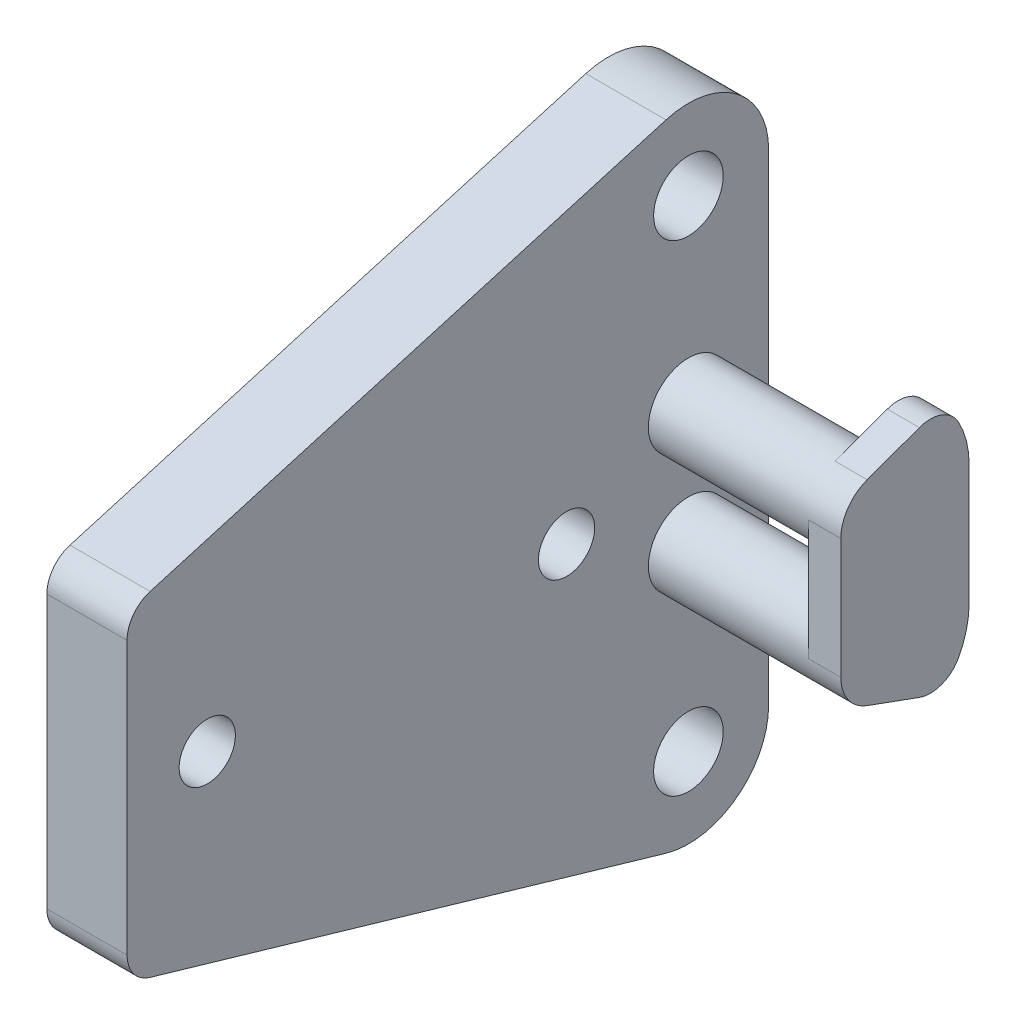
SolidWorks part; units mm, degrees
ref_plane "Front Plane" through (0, 0, 0) normal (0, 0, 1) x (1, 0, 0)
ref_plane "Top Plane" through (0, 0, 0) normal (0, 1, 0) x (1, 0, 0)
ref_plane "Right Plane" through (0, 0, 0) normal (1, 0, 0) x (0, 0, -1)
sketch "Sketch1" plane through (0, 0, 0) normal (1, 0, 0) x (0, 0, -1)
  line L0 (0, 19.05) -> (0, -19.05) construction
  line L1 (0, 19.05) -> (36.0622, 31.3433) construction
  line L2 (36.0622, 31.3433) -> (64.7397, 6.2591) construction
  line L3 (0, -19.05) -> (36.0622, -31.3433) construction
  line L4 (36.0622, -31.3433) -> (64.7397, -6.2591) construction
  line L5 (0, 19.05) -> (-9.0156, 15.9767) construction
  line L6 (0, -19.05) -> (-9.0156, -15.9767) construction
  line L7 (9.6166, 22.3282) -> (9.6166, -22.3282) construction
  line L8 (-9.0156, 15.9767) -> (2.4345, 8.4816) construction
  line L9 (0, 0.3175) -> (-13.3728, 0.3175) construction
  line L10 (-9.0156, -15.9767) -> (2.4345, -8.4816) construction
  line L11 (0, -0.3175) -> (-11.5327, -0.3175) construction
  line L12 (-9.0156, 15.9767) -> (-15.0259, 13.9278) construction
  line L13 (-44.45, 12.7) -> (-44.45, -12.7)
  line L14 (-44.45, -12.7) -> (-1.778, -25.146)
  line L15 (6.35, -19.05) -> (6.35, 19.05)
  line L16 (-34.3516, 0) -> (16.0982, 0) construction
  line L17 (-44.45, 12.7) -> (-1.778, 25.146)
  circle A2 centre (0, 4.7625) radius 3.175 construction
  circle A3 centre (0, -4.7625) radius 3.175 construction
  arc A4 (2.4345, 8.4816) -> (0, 0.3175) centre (0, 4.7625) cw construction
  arc A5 (0, -0.3175) -> (2.4345, -8.4816) centre (0, -4.7625) cw construction
  arc A6 (-1.778, -25.146) -> (6.35, -19.05) centre (0, -19.05) ccw
  arc A7 (-1.778, 25.146) -> (6.35, 19.05) centre (0, 19.05) cw
  circle A8 centre (-38.1, 0) radius 2.2267
  circle A9 centre (-9.652, 0) radius 2.2267
  circle A10 centre (0, -19.05) radius 2.7559
  circle A11 centre (0, 19.05) radius 2.7559
  point P0 (0, 0)
  point P29 (-44.45, 0)
  point P31 (6.35, 0)
  dimension "D10" = 6.35
  dimension "D14" = 1.27
  dimension "D15" = 6.35
  dimension "D16" = 25.4
  dimension "D17" = 6.35
  dimension "D18" = 28.448
  dimension "D20" = 4.4534
  dimension "D22" = 5.5118
  dimension "D2" = 120
  dimension "D3" = 120
  dimension "D4" = 38.1
  dimension "D5" = 38.1
  dimension "D6" = 9.525
  dimension "D7" = 38.1
  dimension "D8" = 10.16
  dimension "D9" = 10.16
  dimension "D11" = 4.7625
  dimension "D12" = 4.7625
  dimension "D13" = 9.525
  dimension "D19" = 6.35
  dimension "D21" = 50.8
extrude "Boss-Extrude1" add sketch "Sketch1" against normal blind 6.35
sketch "Sketch2" plane through (0, 0, 0) normal (1, 0, 0) x (0, 0, -1)
  circle A0 centre (0, -4.7625) radius 3.175 construction
  circle A1 centre (0, 4.7625) radius 3.175 construction
  circle A2 centre (0, -4.7625) radius 3.175
  circle A3 centre (0, 4.7625) radius 3.175
extrude "Boss-Extrude2" add sketch "Sketch2" along normal blind 12.7
sketch "Sketch4" plane through (12.7, 0, 0) normal (1, 0, 0) x (0, 0, -1)
  line L0 (-3.175, 4.7625) -> (-3.175, -4.7625)
  line L2 (6.985, 4.7625) -> (6.985, -4.7625)
  line L3 (4.7606, 9.874) -> (-1.0859, 7.746)
  line L4 (4.7606, -9.874) -> (-1.0859, -7.746)
  arc A0 (4.7606, 9.874) -> (6.985, 4.7625) centre (0, 4.7625) cw
  arc A1 (4.7606, -9.874) -> (6.985, -4.7625) centre (0, -4.7625) ccw
  arc A4 (-3.175, 4.7625) -> (-1.0859, 7.746) centre (0, 4.7625) cw
  arc A5 (-3.175, -4.7625) -> (-1.0859, -7.746) centre (0, -4.7625) ccw
  circle A6 centre (0, 4.7625) radius 3.175 construction
  circle A7 centre (0, -4.7625) radius 3.175 construction
  point P3 (5.5848, 8.9815)
  dimension "D1" = 3.81
  dimension "D2" = 110
  dimension "D3" = 110
extrude "Boss-Extrude3" add sketch "Sketch4" along normal blind 2.54
fillet "Fillet1" radius 2.54 4 edges at (-3.175, -12.7, 44.45) (-3.175, 12.7, 44.45) (13.97, 9.874, -4.7606) (13.97, -9.874, -4.7606)
